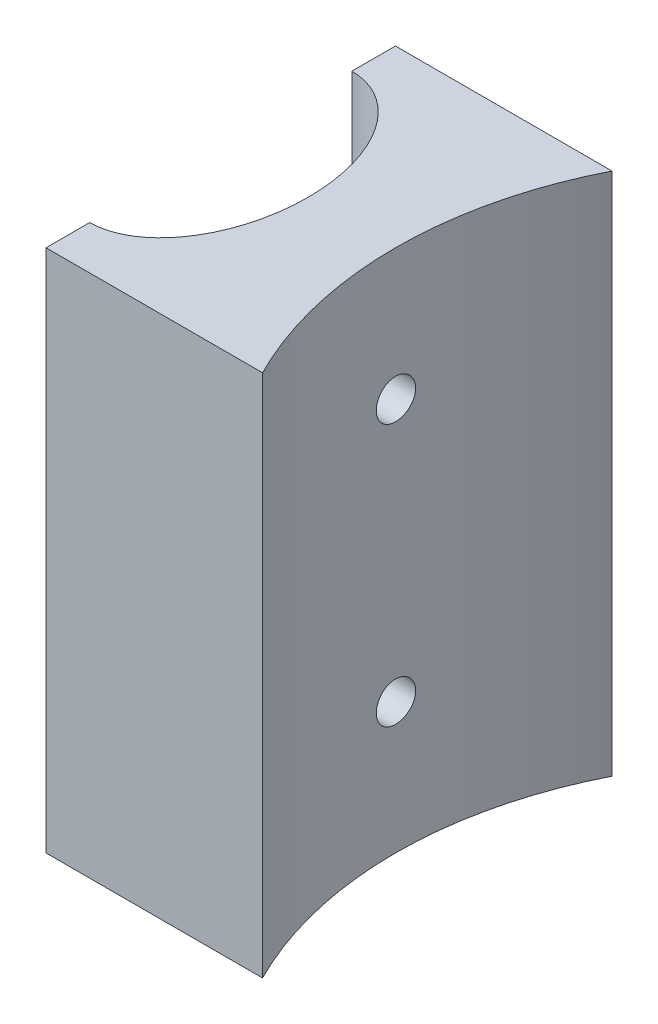
SolidWorks part; units mm, degrees
ref_plane "Front Plane" through (0, 0, 0) normal (0, 0, 1) x (1, 0, 0)
ref_plane "Top Plane" through (0, 0, 0) normal (0, 1, 0) x (1, 0, 0)
ref_plane "Right Plane" through (0, 0, 0) normal (1, 0, 0) x (0, 0, -1)
sketch "Sketch1" plane through (0, 0, 0) normal (0, 1, 0) x (1, 0, 0)
  line L0 (-44.1998, 0) -> (-54.1998, 0) construction
  line L1 (-54.1998, 0) -> (-64.1998, 0) construction
  line L2 (-64.1998, 15) -> (-64.1998, 20)
  line L3 (-64.1998, -15) -> (-64.1998, -20)
  line L4 (-64.1998, 20) -> (-39.4161, 20)
  line L5 (-64.1998, -20) -> (-39.4161, -20)
  circle A0 centre (0, 0) radius 44.1998 construction
  arc A1 (-39.4161, 20) -> (-39.4161, -20) centre (0, 0) ccw
  ellipse E0 centre (-64.1998, 0) end of major axis (-64.1998, 15) minor radius 10
  dimension "D1" = 10
extrude "Boss-Extrude1" add sketch "Sketch1" along normal blind 60 contours E0 L3 L5 A1 L4 L2
sketch "Sketch2" plane through (0, 0, 0) normal (1, 0, 0) x (0, 0, -1)
  line L0 (0, 61.8591) -> (0, -2.4921) construction
sketch "Sketch5" plane through (0, 0, 0) normal (1, 0, 0) x (0, 0, -1)
  line L0 (20, 30) -> (-20, 30) construction
  line L1 (20, 60) -> (20, 0) construction
  line L2 (-20, 60) -> (-20, 0) construction
hole_wizard "M4 Clearance Hole1" positions "Sketch6" profile "Sketch7" hole size "M4" standard "IS"
sketch "Sketch6" plane through (0, 0, 0) normal (1, 0, 0) x (0, 0, -1)
  line L0 (0, 61.8591) -> (0, -2.4921) construction
  line L1 (20, 30) -> (-20, 30) construction
  point P0 (0, 45)
  point P7 (0, 15)
  dimension "D1" = 15
  dimension "D2" = 15
sketch "Sketch7" plane through (0, 45, 0) normal (0, 1, 0) x (0, 0, -1)
  line L0 (0, 0) -> (0, 71.3519)
  line L1 (0, 71.3519) -> (2.25, 70)
  line L2 (2.25, 70) -> (2.25, 0)
  line L5 (2.25, 0) -> (0, 0)
  line L10 (0, 71.3519) -> (-2.25, 70) construction
  line L11 (0, -6.35) -> (0, 107.95) construction
  dimension "Hole Dia." = 4.5
  dimension "Hole Depth" = 70
  dimension "Drill Angle" = 118
